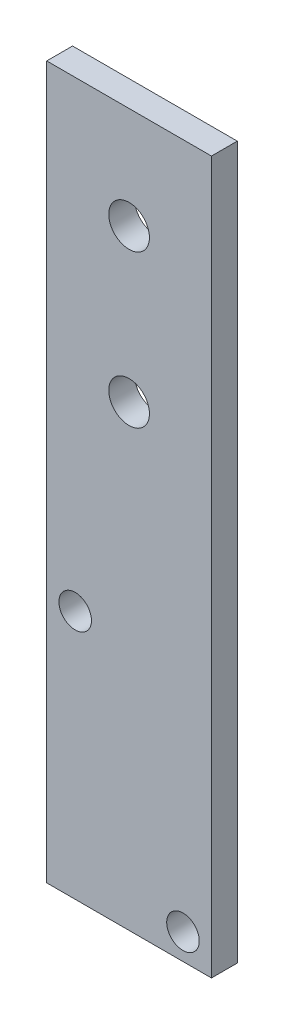
SolidWorks part; units mm, degrees
ref_plane "Front Plane" through (0, 0, 0) normal (0, 0, 1) x (1, 0, 0)
ref_plane "Top Plane" through (0, 0, 0) normal (0, 1, 0) x (1, 0, 0)
ref_plane "Right Plane" through (0, 0, 0) normal (1, 0, 0) x (0, 0, -1)
sketch "Sketch1" plane through (0, 0, 0) normal (0, 0, 1) x (1, 0, 0)
  line L1 (0, 0) -> (16.2, 0)
  line L2 (0, 0) -> (0, 70)
  line L3 (0, 70) -> (16.2, 70)
  line L4 (16.2, 0) -> (16.2, 70)
  dimension "D1" = 16.2
  dimension "D2" = 70
extrude "Boss-Extrude1" add sketch "Sketch1" along normal blind 2.54
sketch "Sketch2" plane through (0, 0, 2.54) normal (0, 0, 1) x (1, 0, 0)
  line L0 (16.2, 0) -> (16.2, 70) construction
  line L1 (0, 0) -> (16.2, 0)
  line L2 (0, 0) -> (0, 2.54)
  line L3 (0, 2.54) -> (16.2, 2.54)
  line L4 (16.2, 0) -> (16.2, 2.54)
  dimension "D1" = 2.54
extrude "Boss-Extrude2" [suppressed] add sketch "Sketch2" along normal blind 10
chamfer "Chamfer1" [suppressed] distance 1 angle 45
sketch "Sketch4" plane through (0, 0, 0) normal (0, 0, -1) x (-1, 0, 0)
  line L0 (0, 0) -> (-16.2, 0) construction
  line L1 (-16.2, 70) -> (0, 70) construction
  line L3 (-8.1, 0) -> (-8.1, 70) construction
  line L4 (0, 0) -> (-16.2, 0) construction
  circle A2 centre (-13.4, 2.54) radius 1.6
  circle A3 centre (-2.8, 24.54) radius 1.6
  dimension "D1" = 22
  dimension "D2" = 2.54
extrude "Cut-Extrude1" cut sketch "Sketch4" against normal blind 2.54
sketch "Sketch5" [suppressed] plane through (0, 2.54, 0) normal (0, 1, 0) x (1, 0, 0)
  line L0 (16.2, -8.04) -> (0, -8.04) construction
  line L1 (16.2, -12.54) -> (16.2, -3.54) construction
  line L2 (0, -12.54) -> (0, -3.54) construction
  circle A0 centre (12.2, -8.04) radius 2
  circle A1 centre (4, -8.04) radius 2
  dimension "D1" = 4
sketch "Sketch6" plane through (0, 0, 2.54) normal (0, 0, 1) x (1, 0, 0)
  line L0 (8.1, 70) -> (8.1, 0) construction
  line L1 (16.2, 70) -> (0, 70) construction
  line L2 (0, 0) -> (16.2, 0) construction
  circle A0 centre (8.1, 60) radius 2
  circle A1 centre (8.1, 45) radius 2
  dimension "D1" = 4
  dimension "D4" = 15
extrude "Cut-Extrude3" cut sketch "Sketch6" against normal through all
